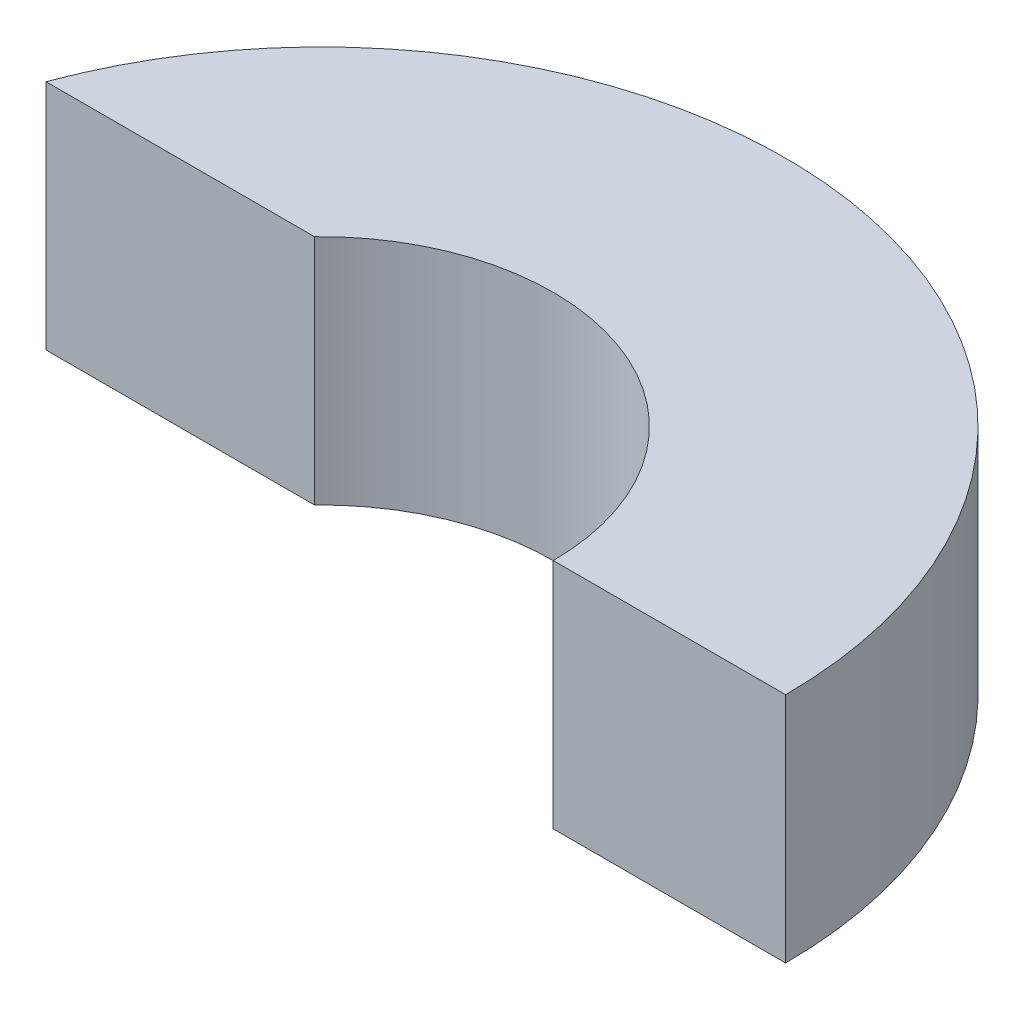
SolidWorks part; units mm, degrees
ref_plane "Front Plane" through (0, 0, 0) normal (0, 0, 1) x (1, 0, 0)
ref_plane "Top Plane" through (0, 0, 0) normal (0, 1, 0) x (1, 0, 0)
ref_plane "Right Plane" through (0, 0, 0) normal (1, 0, 0) x (0, 0, -1)
sketch "Sketch1" plane through (0, 0, 0) normal (0, 1, 0) x (1, 0, 0)
  line L0 (5, 0) -> (10, 0)
  line L2 (-3.6032, 3.4665) -> (-9.3799, 3.4665)
  arc A0 (5, 0) -> (-3.6032, 3.4665) centre (0, 0) ccw
  arc A2 (10, 0) -> (-9.3799, 3.4665) centre (0, 0) ccw
  dimension "D1" = 10
  dimension "D2" = 10
extrude "Boss-Extrude1" add sketch "Sketch1" along normal blind 5
